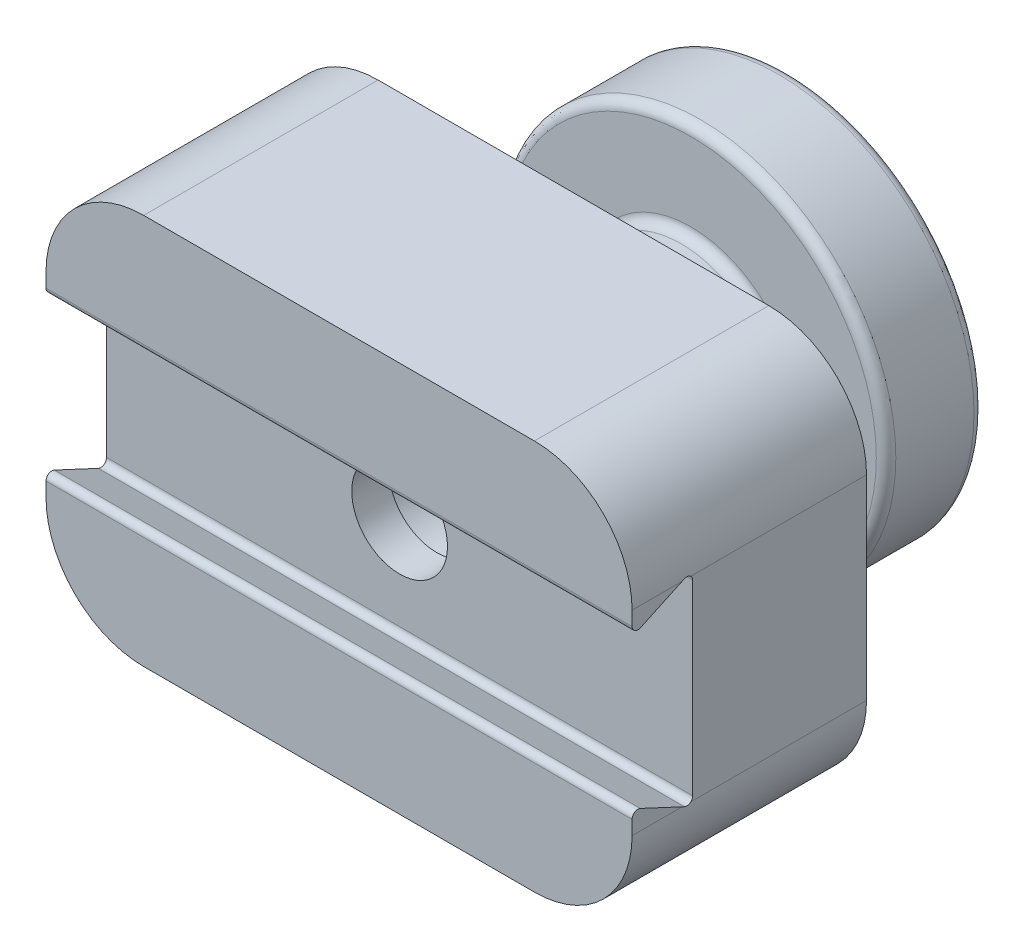
SolidWorks part; units mm, degrees
ref_plane "Front" through (0, 0, 0) normal (0, 0, 1) x (1, 0, 0)
ref_plane "Top" through (0, 0, 0) normal (0, 1, 0) x (1, 0, 0)
ref_plane "Right" through (0, 0, 0) normal (1, 0, 0) x (0, 0, -1)
sketch "Sketch1" plane through (0, 0, 0) normal (0, 0, 1) x (1, 0, 0)
  line L0 (18.3647, 0) -> (-19.4746, 0) construction
  arc A1 (10, 0) -> (-10, 0) centre (0, 0) ccw
  arc A2 (10, 0) -> (-10, 0) centre (0, 0) cw
  point P4 (0, -2.5)
  dimension "D2" = 10
extrude "Boss-Extrude1" add sketch "Sketch1" along normal blind 5
sketch "Sketch2" plane through (0, 0, 0) normal (0, 0, 1) x (1, 0, 0)
  circle A0 centre (0, 0) radius 5
  dimension "D1" = 10
extrude "Boss-Extrude2" add sketch "Sketch2" along normal blind 11
ref_plane "Plane1" through (0, 0, 11) normal (0, 0, 1) x (1, 0, 0)
ref_point "Point1"
sketch "Sketch3" plane through (0, 0, 11) normal (0, 0, 1) x (1, 0, 0)
  line L1 (-15, 10) -> (15, 10)
  line L2 (-15, 10) -> (-15, -10)
  line L3 (-15, -10) -> (15, -10)
  line L4 (15, 10) -> (15, -10)
  line L5 (-15, 10) -> (15, -10) construction
  line L6 (-15, -10) -> (15, 10) construction
  point P0 (0, 0)
  dimension "D1" = 20
  dimension "D2" = 30
  dimension "D6" = 30
extrude "Boss-Extrude3" add sketch "Sketch3" along normal blind 12
ref_plane "Plane2" through (-10, 0, 0) normal (1, 0, 0) x (0, 0, -1)
sketch "Sketch5" plane through (-10, 0, 0) normal (1, 0, 0) x (0, 0, -1)
  line L0 (-23, 3.8044) -> (-19.9, 5.25)
  line L2 (-19.9, 5.25) -> (-19.9, -5.25)
  line L3 (-19.9, -5.25) -> (-23, -3.8044)
  line L4 (-23, -3.8044) -> (-23, 3.8044)
  line L5 (-23, 0) -> (-19.9, 0) construction
  line L7 (-23, 10) -> (-23, -10) construction
  line L8 (-23, 10) -> (-11, 10) construction
  line L9 (-23, -10) -> (-23, 10) construction
  dimension "D1" = 10.5
  dimension "D2" = 10
  dimension "D3" = 3.1
  dimension "D4" = 5.25
  dimension "D5" = 3.1
  dimension "D6" = 3.8044
  dimension "D8" = 65
extrude "Cut-Extrude1" cut sketch "Sketch5" along normal through all both and the other way through all
sketch "Sketch6" plane through (0, 0, 23) normal (0, 0, 1) x (1, 0, 0)
  circle A0 centre (0, 0) radius 2.45
  dimension "D1" = 4.9
extrude "Cut-Extrude2" cut sketch "Sketch6" against normal blind 5
pattern_linear "LPattern1" [suppressed] count 3 spacing 7
fillet "Fillet1" radius 0.3 4 edges at (0, -5.25, 19.9) (0, -3.8044, 23) (0, 5.25, 19.9) (0, 3.8044, 23)
fillet "Fillet2" radius 5 4 edges at (-15, -10, 17) (15, -10, 17) (15, 10, 17) (-15, 10, 17)
fillet "Fillet3" radius 0.5 4 edges at (10, 0, 0) (-10, 0, 5) (-5, 0, 5) (5, 0, 11)
sketch "Sketch7" plane through (0, 0, 18) normal (0, 0, 1) x (1, 0, 0)
  circle A0 centre (0, 0) radius 2.9
  dimension "D1" = 5.8
extrude "Cut-Extrude3" cut sketch "Sketch7" against normal blind 6
